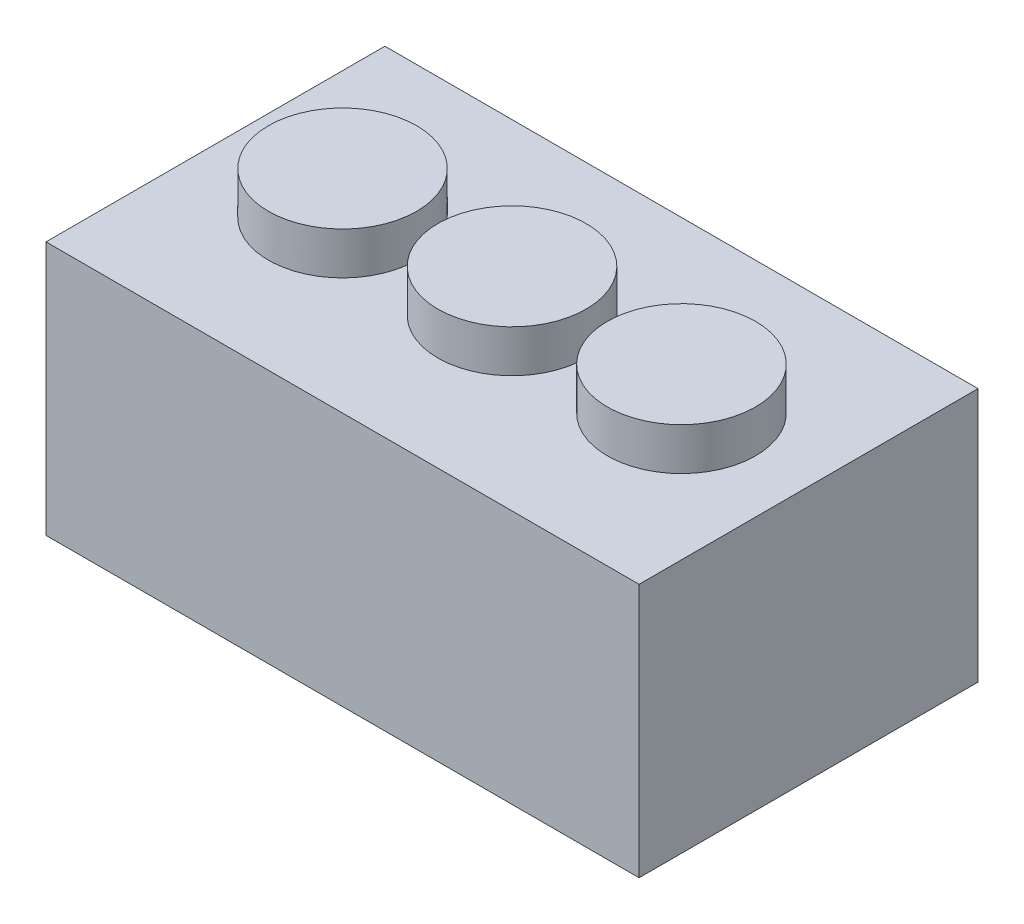
SolidWorks part; units mm, degrees
ref_plane "Alzado" through (0, 0, 0) normal (0, 0, 1) x (1, 0, 0)
ref_plane "Planta" through (0, 0, 0) normal (0, 1, 0) x (1, 0, 0)
ref_plane "Vista lateral" through (0, 0, 0) normal (1, 0, 0) x (0, 0, -1)
sketch "Croquis1" plane through (0, 0, 0) normal (0, 1, 0) x (1, 0, 0)
  line L1 (-70, -40) -> (70, -40)
  line L2 (-70, -40) -> (-70, 40)
  line L3 (-70, 40) -> (70, 40)
  line L4 (70, -40) -> (70, 40)
  line L5 (-70, -40) -> (70, 40) construction
  line L6 (-70, 40) -> (70, -40) construction
  point P0 (0, 0)
  dimension "D1" = 140
  dimension "D2" = 80
extrude "Saliente-Extruir1" add sketch "Croquis1" along normal blind 60
sketch "Croquis2" plane through (0, 60, 0) normal (0, 1, 0) x (1, 0, 0)
  line L0 (0, 36.1463) -> (0, -40) construction
  line L1 (-70, -40) -> (70, -40) construction
  line L2 (-69.2552, 0) -> (66.2177, 0) construction
  circle A0 centre (0, 0) radius 17.5
  circle A1 centre (-40, 0) radius 17.5
  circle A2 centre (40, 0) radius 17.5
  point P9 (0, 0)
  dimension "D1" = 35
  dimension "D3" = 35
  dimension "D2" = 40
extrude "Saliente-Extruir2" add sketch "Croquis2" along normal blind 10
shell "Vaciado1" thickness 2
sketch "Croquis3" plane through (0, 58, 0) normal (0, -1, 0) x (1, 0, 0)
  line L0 (68, 38) -> (68, -38) construction
  line L1 (-68, -2) -> (-19.3972, -2)
  line L2 (-68, -2) -> (-68, 2)
  line L3 (-68, 2) -> (-19.3972, 2)
  line L4 (68, -2) -> (68, 2)
  line L5 (-4.4615, 0) -> (9.8378, 0) construction
  line L11 (19.3972, 2) -> (68, 2)
  line L14 (19.3972, -2) -> (68, -2)
  circle A1 centre (0, 0) radius 15.5
  arc A2 (-19.3972, -2) -> (19.3972, -2) centre (0, 0) ccw
  arc A3 (19.3972, 2) -> (-19.3972, 2) centre (0, 0) ccw
  dimension "D1" = 31
  dimension "D2" = 19.5
  dimension "D3" = 4
  dimension "D4" = 48.6028
  dimension "D5" = 48.6028
  dimension "D6" = 4
extrude "Saliente-Extruir3" add sketch "Croquis3" along normal up to surface (58 mm away) up to face at (0, 0, 0)
